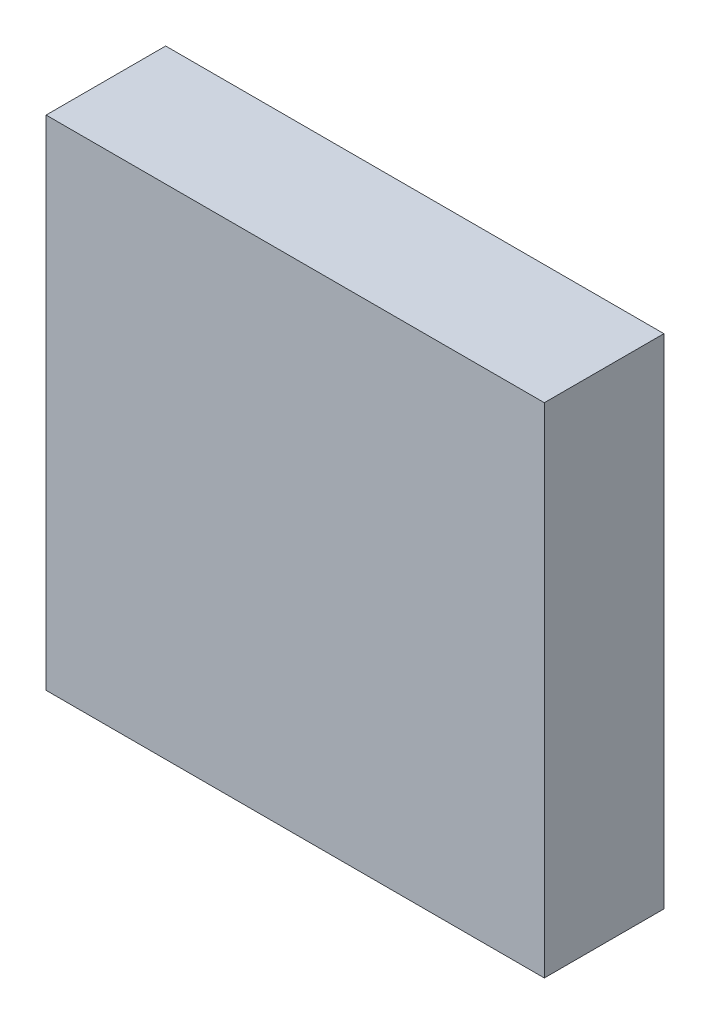
SolidWorks part; units mm, degrees
ref_plane "前视基准面" through (0, 0, 0) normal (0, 0, 1) x (1, 0, 0)
ref_plane "上视基准面" through (0, 0, 0) normal (0, 1, 0) x (1, 0, 0)
ref_plane "右视基准面" through (0, 0, 0) normal (1, 0, 0) x (0, 0, -1)
sketch "草图1" plane through (0, 0, 0) normal (0, 0, 1) x (1, 0, 0)
  line L0 (203.0052, 77.2932) -> (238.3226, 77.2932) construction
  line L1 (220.8088, 94.6175) -> (220.8088, 60.0622) construction
  line L2 (208.3088, 77.2932) -> (208.3088, 89.7932)
  line L3 (208.3088, 89.7932) -> (233.3088, 89.7932)
  line L4 (233.3088, 89.7932) -> (233.3088, 64.7932)
  line L5 (233.3088, 64.7932) -> (208.3088, 64.7932)
  line L6 (208.3088, 64.7932) -> (208.3088, 77.2932)
extrude "凸台-拉伸1" add sketch "草图1" along normal blind 6
